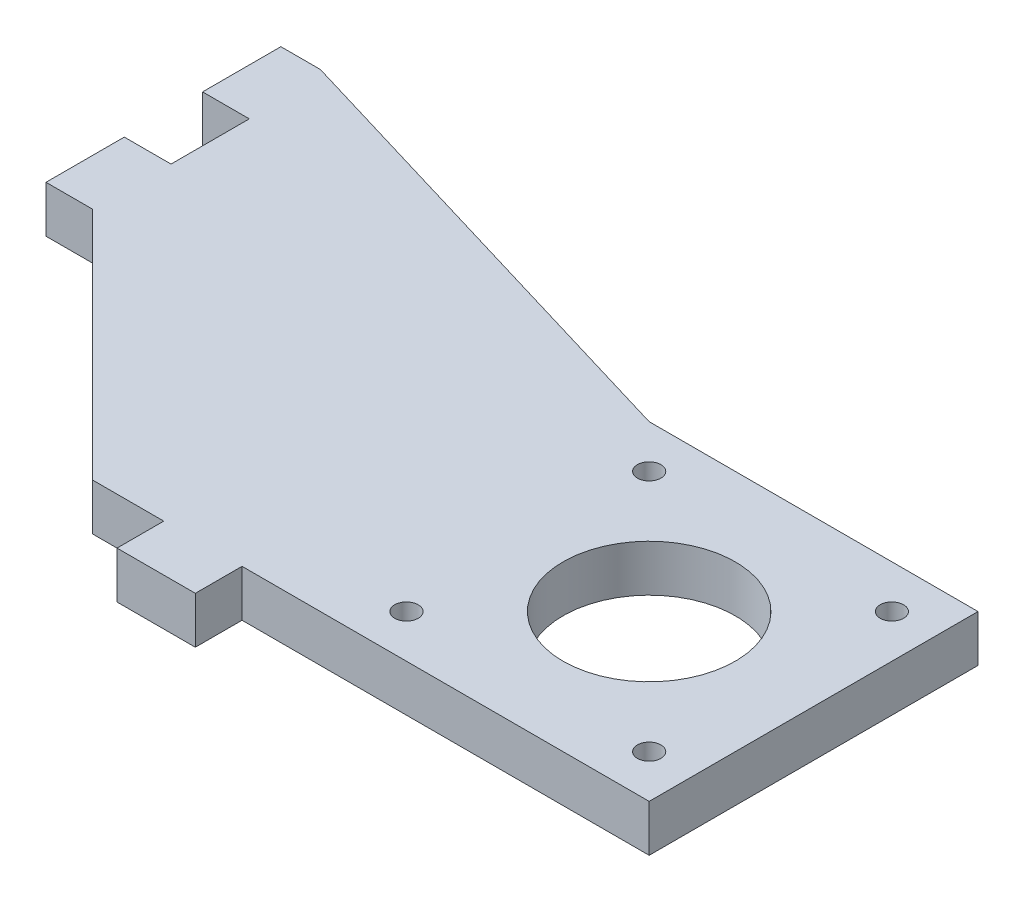
SolidWorks part; units mm, degrees
ref_plane "Front Plane" through (0, 0, 0) normal (0, 0, 1) x (1, 0, 0)
ref_plane "Top Plane" through (0, 0, 0) normal (0, 1, 0) x (1, 0, 0)
ref_plane "Right Plane" through (0, 0, 0) normal (1, 0, 0) x (0, 0, -1)
sketch "Sketch1" plane through (0, 0, 0) normal (0, 1, 0) x (1, 0, 0)
  line L0 (0, 0) -> (-5.969, 0)
  line L1 (-5.969, 0) -> (-5.969, 10)
  line L2 (-5.969, 10) -> (0, 10)
  line L3 (0, 10) -> (0, 20)
  line L4 (0, 20) -> (-5.969, 20)
  line L5 (-5.969, 20) -> (-5.969, 30)
  line L6 (-5.969, 30) -> (-0.928, 30)
  line L7 (-0.928, 30) -> (59.031, -29.959)
  line L8 (59.031, -29.959) -> (49.031, -29.959)
  line L9 (49.031, -29.959) -> (49.031, -35.928)
  line L10 (49.031, -35.928) -> (39.031, -35.928)
  line L11 (39.031, -35.928) -> (39.031, -29.959)
  line L12 (39.031, -29.959) -> (29.959, -29.959)
  line L13 (29.959, -29.959) -> (0, 0)
  dimension "D1" = 5.969
  dimension "D2" = 10
  dimension "D3" = 65
  dimension "D4" = 10
  dimension "D5" = 65.928
  dimension "D6" = 135
extrude "Boss-Extrude1" add sketch "Sketch1" along normal blind 5.969
sketch "Sketch2" plane through (0, 5.969, 0) normal (0, 1, 0) x (1, 0, 0)
  line L0 (59.031, -29.959) -> (-0.928, 30) construction
  line L1 (59.031, -29.959) -> (101.031, -29.959)
  line L2 (59.031, -29.959) -> (59.031, 12.041) construction
  line L3 (59.031, 12.041) -> (101.031, 12.041)
  line L4 (101.031, -29.959) -> (101.031, 12.041)
  line L5 (59.031, -8.959) -> (101.031, -8.959) construction
  line L6 (80.031, 12.041) -> (80.031, -29.959) construction
  line L7 (49.031, -29.959) -> (59.031, -29.959) construction
  line L8 (64.531, 6.541) -> (59.031, 6.541) construction
  line L9 (64.531, 6.541) -> (64.531, 12.041) construction
  line L10 (95.531, -24.459) -> (95.531, -29.959) construction
  line L11 (95.531, -24.459) -> (101.031, -24.459) construction
  line L12 (59.031, 12.041) -> (-0.928, 30)
  line L13 (-0.928, 30) -> (59.031, -29.959)
  circle A0 centre (80.031, -8.959) radius 11
  circle A1 centre (64.531, 6.541) radius 1.5
  circle A2 centre (95.531, 6.541) radius 1.5
  circle A3 centre (64.531, -24.459) radius 1.5
  circle A4 centre (95.531, -24.459) radius 1.5
  dimension "D3" = 22
  dimension "D4" = 31
  dimension "D5" = 3
  dimension "D1" = 42
  dimension "D2" = 42
extrude "Boss-Extrude2" add sketch "Sketch2" against normal blind 5.969
